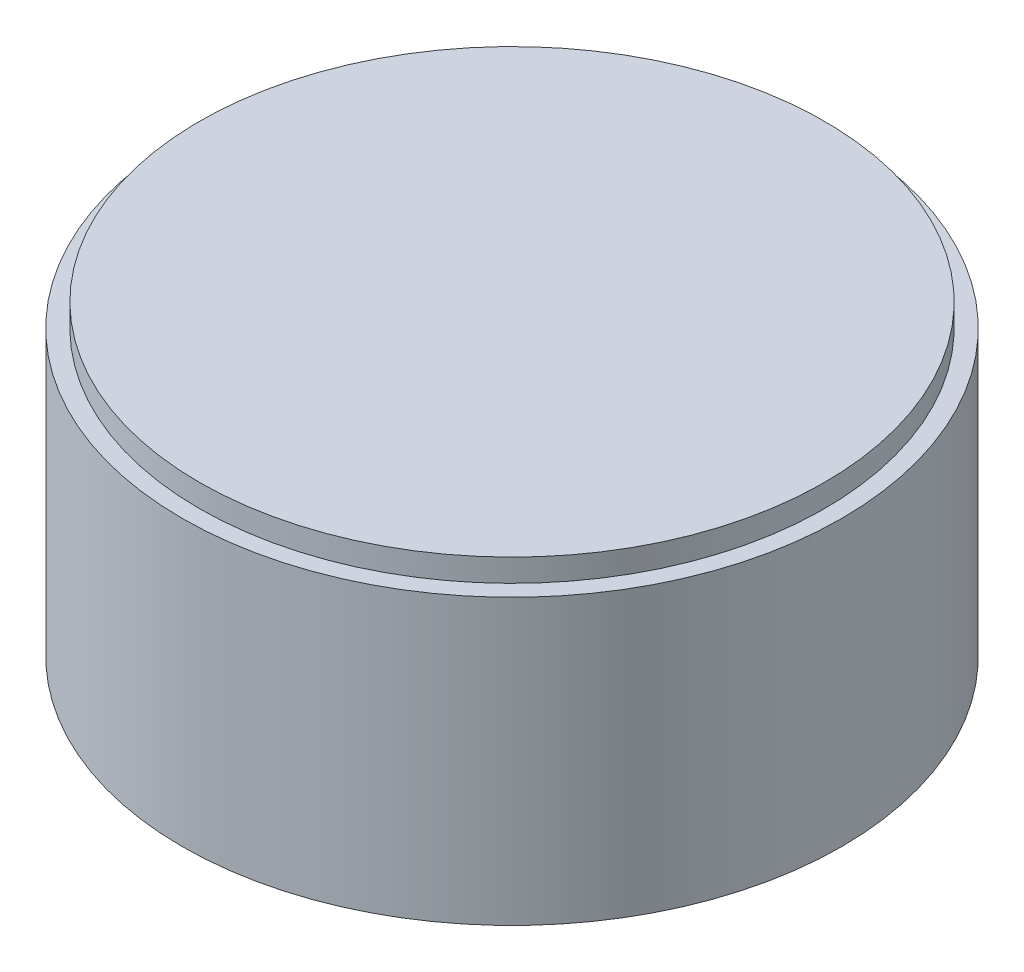
SolidWorks part; units mm, degrees
ref_plane "Front Plane" through (0, 0, 0) normal (0, 0, 1) x (1, 0, 0)
ref_plane "Top Plane" through (0, 0, 0) normal (0, 1, 0) x (1, 0, 0)
ref_plane "Right Plane" through (0, 0, 0) normal (1, 0, 0) x (0, 0, -1)
sketch "Sketch1" plane through (0, 0, 0) normal (0, 1, 0) x (1, 0, 0)
  circle A0 centre (0, 0) radius 5.8
  dimension "D1" = 11.6
extrude "Boss-Extrude1" add sketch "Sketch1" along normal blind 5
sketch "Sketch2" plane through (0, 5, 0) normal (0, 1, 0) x (1, 0, 0)
  circle A0 centre (0, 0) radius 5.5
  dimension "D1" = 11
extrude "Boss-Extrude2" add sketch "Sketch2" along normal blind 0.4
